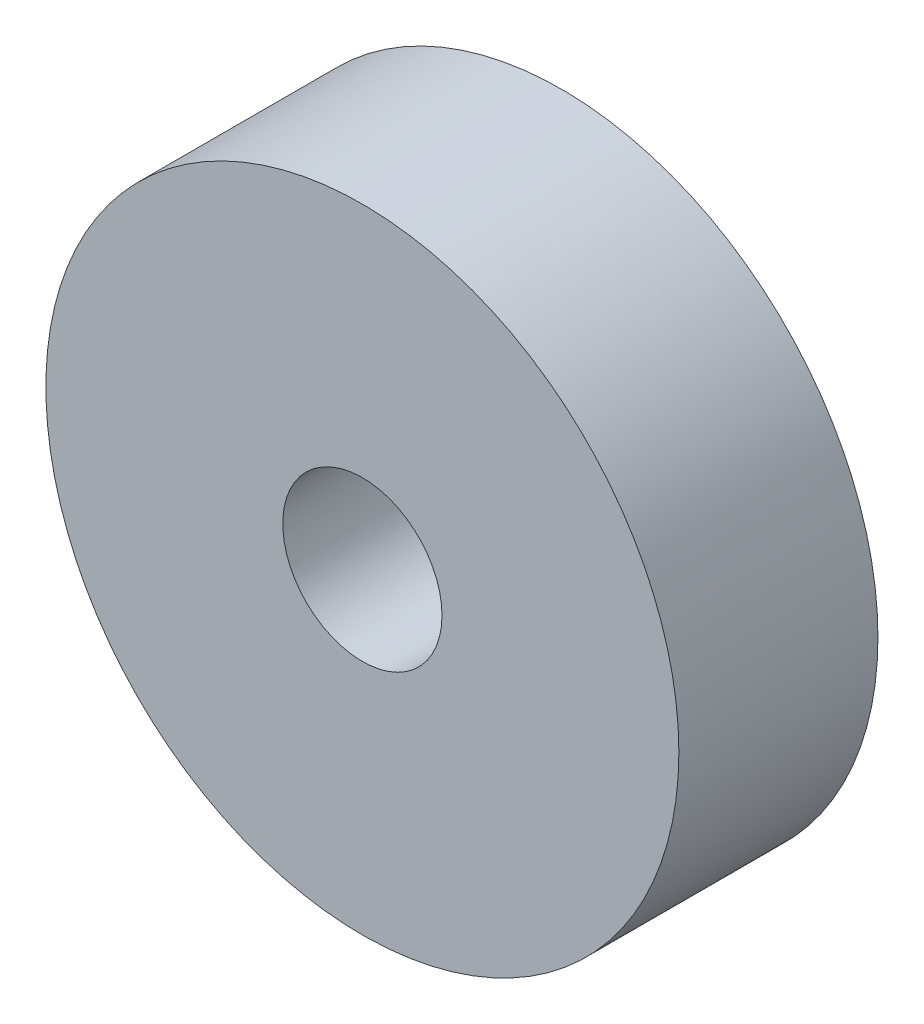
SolidWorks part; units mm, degrees
ref_plane "Plan de face" through (0, 0, 0) normal (0, 0, 1) x (1, 0, 0)
ref_plane "Plan de dessus" through (0, 0, 0) normal (0, 1, 0) x (1, 0, 0)
ref_plane "Plan de droite" through (0, 0, 0) normal (1, 0, 0) x (0, 0, -1)
sketch "Esquisse1" plane through (0, 0, 0) normal (0, 0, 1) x (1, 0, 0)
  circle A0 centre (37.9449, 25.3523) radius 15.9
  circle A1 centre (37.9449, 25.3523) radius 4
  dimension "D1" = 8
  dimension "D2" = 31.8
extrude "Boss.-Extru.1" add sketch "Esquisse1" along normal blind 10
